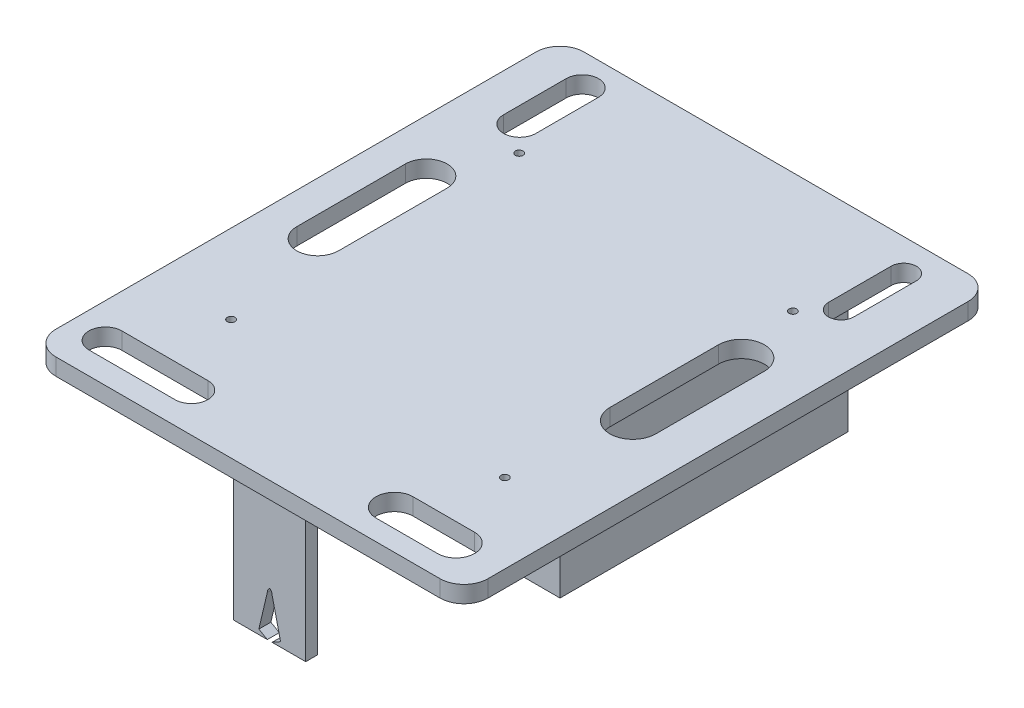
SolidWorks part; units mm, degrees
ref_plane "前视基准面" through (0, 0, 0) normal (0, 0, 1) x (1, 0, 0)
ref_plane "上视基准面" through (0, 0, 0) normal (0, 1, 0) x (1, 0, 0)
ref_plane "右视基准面" through (0, 0, 0) normal (1, 0, 0) x (0, 0, -1)
sketch "草图1" plane through (0, 0, 0) normal (0, 1, 0) x (1, 0, 0)
  line L0 (-95.2597, 129.0909) -> (-62.2597, 129.0909) construction
  line L1 (-85.2597, 139.0909) -> (74.7403, 139.0909)
  line L2 (-95.2597, 129.0909) -> (-95.2597, -70.9091)
  line L3 (-85.2597, -80.9091) -> (74.7403, -80.9091)
  line L4 (84.7403, 129.0909) -> (84.7403, -70.9091)
  line L5 (-62.2597, 139.0909) -> (-62.2597, 89.0909) construction
  line L6 (84.7403, 129.0909) -> (51.7403, 129.0909) construction
  line L7 (51.7403, 139.0909) -> (51.7403, 89.0909) construction
  line L8 (-95.2597, -70.9091) -> (-62.2597, -70.9091) construction
  line L9 (-62.2597, -80.9091) -> (-62.2597, -30.9091) construction
  line L10 (84.7403, -70.9091) -> (51.7403, -70.9091) construction
  line L11 (51.7403, -70.9091) -> (51.7403, -80.9091) construction
  line L12 (51.7403, -80.9091) -> (51.7403, -30.9091) construction
  arc A0 (-85.2597, 139.0909) -> (-95.2597, 129.0909) centre (-85.2597, 129.0909) ccw
  arc A1 (74.7403, 139.0909) -> (84.7403, 129.0909) centre (74.7403, 129.0909) cw
  arc A2 (74.7403, -80.9091) -> (84.7403, -70.9091) centre (74.7403, -70.9091) ccw
  arc A3 (-95.2597, -70.9091) -> (-85.2597, -80.9091) centre (-85.2597, -70.9091) ccw
  circle A4 centre (-62.2597, 89.0909) radius 1.6
  circle A5 centre (51.7403, 89.0909) radius 1.6
  circle A6 centre (-62.2597, -30.9091) radius 1.6
  circle A7 centre (51.7403, -30.9091) radius 1.6
  point P6 (-95.2597, 139.0909)
  point P9 (84.7403, 139.0909)
  point P14 (-95.2597, -80.9091)
  dimension "D3" = 10
  dimension "D4" = 10
  dimension "D5" = 10
  dimension "D6" = 10
  dimension "D1" = 180
  dimension "D2" = 220
extrude "凸台-拉伸1" add sketch "草图1" along normal blind 7
sketch "草图2" plane through (0, 0, 0) normal (0, -1, 0) x (1, 0, 0)
  line L0 (-5.2597, 80.9091) -> (-5.2597, -139.0909) construction
  line L1 (-85.2597, 80.9091) -> (74.7403, 80.9091) construction
  line L2 (74.7403, -139.0909) -> (-85.2597, -139.0909) construction
  line L3 (-95.2597, -29.0909) -> (84.7403, -29.0909) construction
  line L4 (-95.2597, -129.0909) -> (-95.2597, 70.9091) construction
  line L5 (84.7403, 70.9091) -> (84.7403, -129.0909) construction
  line L6 (-5.2597, -29.0909) -> (-45.2597, -29.0909) construction
  line L7 (-5.2597, -29.0909) -> (34.7403, -29.0909) construction
  line L8 (-45.2597, -29.0909) -> (-45.2597, -119.0909) construction
  line L9 (-45.2597, -119.0909) -> (34.7403, -119.0909) construction
  line L10 (34.7403, -119.0909) -> (34.7403, -29.0909) construction
  line L11 (34.7403, -29.0909) -> (-45.2597, -29.0909) construction
  line L12 (-45.2597, -29.0909) -> (-45.2597, -9.0909) construction
  line L13 (-45.2597, -9.0909) -> (34.7403, -9.0909) construction
  line L14 (34.7403, -9.0909) -> (34.7403, -29.0909) construction
  line L15 (-45.2597, -9.0909) -> (-50.2597, -9.0909) construction
  line L16 (34.7403, -9.0909) -> (-45.2597, -9.0909)
  line L17 (34.7403, -9.0909) -> (34.7403, -119.0909)
  line L18 (34.7403, -119.0909) -> (-45.2597, -119.0909)
  line L19 (-45.2597, -9.0909) -> (-45.2597, -119.0909)
  line L20 (-45.2597, -9.0909) -> (-45.2597, -4.0909) construction
  line L21 (34.7403, -119.0909) -> (34.7403, -124.0909) construction
  line L22 (34.7403, -119.0909) -> (39.7403, -119.0909) construction
  line L24 (39.7403, -124.0909) -> (-50.2597, -124.0909)
  line L25 (39.7403, -124.0909) -> (39.7403, -4.0909)
  line L26 (39.7403, -4.0909) -> (-50.2597, -4.0909)
  line L27 (-50.2597, -124.0909) -> (-50.2597, -4.0909)
extrude "凸台-拉伸2" add sketch "草图2" along normal blind 60
sketch "草图3" plane through (0, 0, 0) normal (0, -1, 0) x (1, 0, 0)
  line L0 (-5.2597, 80.9091) -> (-5.2597, 7.1374) construction
  line L1 (-85.2597, 80.9091) -> (74.7403, 80.9091) construction
  line L2 (-5.2597, 7.1374) -> (-30.2597, 7.1374) construction
  line L3 (-5.2597, 7.1374) -> (19.7403, 7.1374) construction
  line L4 (-30.2597, 7.1374) -> (-30.2597, 37.1374) construction
  line L5 (-30.2597, 37.1374) -> (19.7403, 37.1374) construction
  line L6 (19.7403, 37.1374) -> (19.7403, 7.1374) construction
  line L7 (-30.2597, 37.1374) -> (-33.2597, 37.1374) construction
  line L8 (-30.2597, 7.1374) -> (19.7403, 7.1374)
  line L9 (-30.2597, 7.1374) -> (-30.2597, 37.1374)
  line L10 (-30.2597, 37.1374) -> (19.7403, 37.1374)
  line L11 (19.7403, 7.1374) -> (19.7403, 37.1374)
  line L12 (-30.2597, 37.1374) -> (-30.2597, 40.1374) construction
  line L13 (19.7403, 7.1374) -> (19.7403, 4.1374) construction
  line L14 (19.7403, 7.1374) -> (22.7403, 7.1374) construction
  line L16 (-33.2597, 40.1374) -> (22.7403, 40.1374)
  line L17 (-33.2597, 40.1374) -> (-33.2597, 4.1374)
  line L18 (-33.2597, 4.1374) -> (22.7403, 4.1374)
  line L19 (22.7403, 40.1374) -> (22.7403, 4.1374)
extrude "凸台-拉伸3" add sketch "草图3" along normal blind 10
sketch "草图5" plane through (0, -10, 0) normal (0, -1, 0) x (1, 0, 0)
  line L0 (-33.2597, 4.1374) -> (-33.2597, 7.1374)
  line L1 (-33.2597, 40.1374) -> (-33.2597, 4.1374) construction
  line L2 (-33.2597, 7.1374) -> (22.7403, 7.1374)
  line L3 (22.7403, 4.1374) -> (22.7403, 40.1374) construction
  line L4 (22.7403, 7.1374) -> (22.7403, 4.1374)
  line L5 (22.7403, 4.1374) -> (-33.2597, 4.1374)
extrude "凸台-拉伸4" add sketch "草图5" along normal blind 20
sketch "草图6" plane through (0, 0, 0) normal (0, -1, 0) x (1, 0, 0)
  line L0 (-5.2597, 80.9091) -> (-5.2597, 71.8328) construction
  line L1 (-85.2597, 80.9091) -> (74.7403, 80.9091) construction
  line L2 (-5.2597, 71.8328) -> (-5.2597, 66.8328) construction
  line L3 (-5.2597, 66.8328) -> (9.7403, 66.8328) construction
  line L4 (-5.2597, 66.8328) -> (-20.2597, 66.8328) construction
  line L5 (-20.2597, 66.8328) -> (-20.2597, 71.8328) construction
  line L6 (-20.2597, 71.8328) -> (9.7403, 71.8328) construction
  line L8 (9.7403, 71.8328) -> (-20.2597, 71.8328)
  line L9 (9.7403, 71.8328) -> (9.7403, 66.8328)
  line L10 (9.7403, 66.8328) -> (-20.2597, 66.8328)
  line L11 (-20.2597, 71.8328) -> (-20.2597, 66.8328)
extrude "凸台-拉伸5" add sketch "草图6" along normal blind 60
sketch "草图8" plane through (0, 0, 71.8328) normal (0, 0, 1) x (1, 0, 0)
  line L0 (9.7403, -60) -> (-3.7597, -60) construction
  line L1 (9.7403, -60) -> (-20.2597, -60) construction
  line L2 (-20.2597, -60) -> (-6.7597, -60) construction
  line L3 (-5.2597, 0) -> (-5.2597, -60) construction
  line L4 (9.7403, 0) -> (-20.2597, 0) construction
  line L5 (-5.2597, -60) -> (-5.2597, -41) construction
  line L6 (-5.2597, -60) -> (-10.2597, -60) construction
  line L7 (-5.2597, -60) -> (-0.2597, -60) construction
  line L8 (-5.2597, -41) -> (-6.2597, -41) construction
  line L9 (-5.2597, -41) -> (-4.2597, -41) construction
  line L10 (-5.2597, -41) -> (-5.2597, -43) construction
  line L11 (-5.2597, -43) -> (-6.2597, -43) construction
  line L12 (-6.2597, -43) -> (-5.2597, -43) construction
  line L13 (-5.2597, -43) -> (-4.2597, -43) construction
  line L14 (-6.2597, -43) -> (-10.2597, -60)
  line L15 (-4.2597, -43) -> (-0.2597, -60)
  line L16 (-10.2597, -60) -> (-0.2597, -60)
  arc A0 (-6.2597, -43) -> (-5.2597, -41) centre (-3.7597, -43) cw
  arc A1 (-4.2597, -43) -> (-5.2597, -41) centre (-6.7597, -43) ccw
  dimension "D1" = 2
extrude "切除-拉伸1" cut sketch "草图8" against normal blind 10
sketch "草图9" plane through (0, 0, 71.8328) normal (0, 0, 1) x (1, 0, 0)
  line L0 (-10.2597, -60) -> (-6.2597, -60) construction
  line L1 (39.7403, -60) -> (-50.2597, -60) construction
  line L2 (-0.2597, -60) -> (-4.2597, -60) construction
  line L3 (-6.2597, -60) -> (-6.2597, -58) construction
  line L4 (-4.2597, -60) -> (-4.2597, -58) construction
  line L5 (-6.2597, -60) -> (-9.7892, -58)
  line L6 (-6.2597, -43) -> (-10.2597, -60) construction
  line L7 (-9.7892, -58) -> (-10.2597, -60)
  line L8 (-10.2597, -60) -> (-6.2597, -60)
  line L9 (-4.2597, -60) -> (-0.2597, -60)
  line L10 (-4.2597, -60) -> (-0.7303, -58)
  line L11 (-0.2597, -60) -> (-4.2597, -43) construction
  line L12 (-0.7303, -58) -> (-0.2597, -60)
extrude "凸台-拉伸6" add sketch "草图9" against normal blind 5
sketch "草图10" plane through (0, 0, 0) normal (0, -1, 0) x (1, 0, 0)
  line L0 (-73.3698, -16.2598) -> (-73.3698, -61.4888) construction
  line L1 (-64.659, -16.2598) -> (-64.659, -61.4888)
  line L2 (-82.0806, -16.2598) -> (-82.0806, -61.4888)
  line L3 (57.9069, -16.2598) -> (57.9069, -61.4888) construction
  line L4 (67.4592, -16.2598) -> (67.4592, -61.4888)
  line L5 (48.3545, -16.2598) -> (48.3545, -61.4888)
  arc A0 (-64.659, -16.2598) -> (-82.0806, -16.2598) centre (-73.3698, -16.2598) ccw
  arc A1 (-82.0806, -61.4888) -> (-64.659, -61.4888) centre (-73.3698, -61.4888) ccw
  arc A2 (67.4592, -16.2598) -> (48.3545, -16.2598) centre (57.9069, -16.2598) ccw
  arc A3 (48.3545, -61.4888) -> (67.4592, -61.4888) centre (57.9069, -61.4888) ccw
  point P2 (-73.3698, -38.8743)
  point P9 (57.9069, -38.8743)
extrude "切除-拉伸2" cut sketch "草图10" against normal blind 10
sketch "草图11" plane through (0, 0, 0) normal (0, -1, 0) x (1, 0, 0)
  line L0 (-80.8928, 64.6559) -> (-45.0446, 64.6559) construction
  line L1 (-80.8928, 71.524) -> (-45.0446, 71.524)
  line L2 (-80.8928, 57.7878) -> (-45.0446, 57.7878)
  line L3 (39.5504, 64.6559) -> (65.1801, 64.6559) construction
  line L4 (39.5504, 72.3616) -> (65.1801, 72.3616)
  line L5 (39.5504, 56.9502) -> (65.1801, 56.9502)
  arc A0 (-80.8928, 71.524) -> (-80.8928, 57.7878) centre (-80.8928, 64.6559) ccw
  arc A1 (-45.0446, 57.7878) -> (-45.0446, 71.524) centre (-45.0446, 64.6559) ccw
  arc A2 (39.5504, 72.3616) -> (39.5504, 56.9502) centre (39.5504, 64.6559) ccw
  arc A3 (65.1801, 56.9502) -> (65.1801, 72.3616) centre (65.1801, 64.6559) ccw
  point P2 (-62.9687, 64.6559)
  point P7 (52.3653, 64.6559)
extrude "切除-拉伸3" cut sketch "草图11" against normal blind 10
sketch "草图12" plane through (0, 0, 0) normal (0, -1, 0) x (1, 0, 0)
  line L0 (-72.6422, -99.696) -> (-72.6422, -125.7701) construction
  line L1 (-65.9039, -99.696) -> (-65.9039, -125.7701)
  line L2 (-79.3804, -99.696) -> (-79.3804, -125.7701)
  line L3 (61.2438, -99.696) -> (61.2438, -125.7701) construction
  line L4 (66.5172, -99.696) -> (66.5172, -125.7701)
  line L5 (55.9704, -99.696) -> (55.9704, -125.7701)
  arc A0 (-65.9039, -99.696) -> (-79.3804, -99.696) centre (-72.6422, -99.696) ccw
  arc A1 (-79.3804, -125.7701) -> (-65.9039, -125.7701) centre (-72.6422, -125.7701) ccw
  arc A2 (66.5172, -99.696) -> (55.9704, -99.696) centre (61.2438, -99.696) ccw
  arc A3 (55.9704, -125.7701) -> (66.5172, -125.7701) centre (61.2438, -125.7701) ccw
  point P2 (-72.6422, -112.733)
  point P7 (61.2438, -112.733)
extrude "切除-拉伸4" cut sketch "草图12" against normal blind 10
